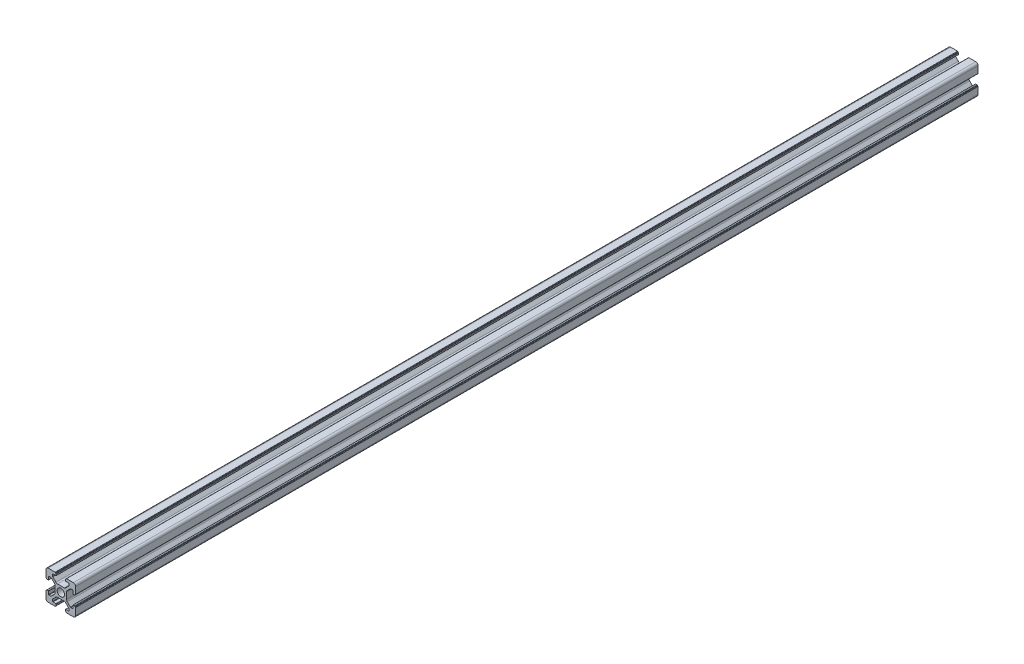
SolidWorks part; units mm, degrees
ref_plane "前视基准面" through (0, 0, 0) normal (0, 0, 1) x (1, 0, 0)
ref_plane "上视基准面" through (0, 0, 0) normal (0, 1, 0) x (1, 0, 0)
ref_plane "右视基准面" through (0, 0, 0) normal (1, 0, 0) x (0, 0, -1)
sketch "草图1" plane through (0, 0, 0) normal (0, 0, 1) x (1, 0, 0)
  line L0 (0, 0) -> (0, 5.5) construction
  line L1 (-8.5023, -10.0023) -> (-3.85, -10.0023)
  line L2 (-10.0023, -8.5023) -> (-10.0023, -3.85)
  line L3 (-8.5023, 10.0023) -> (-3.85, 10.0023)
  line L4 (10.0023, -8.5023) -> (10.0023, -3.85)
  line L5 (-10.0023, -10.0023) -> (10.0023, 10.0023) construction
  line L6 (-10.0023, 10.0023) -> (10.0023, -10.0023) construction
  line L7 (-2.218, -3.9) -> (2.218, -3.9)
  line L8 (-3.9, -2.218) -> (-3.9, 2.218)
  line L9 (-2.218, 3.9) -> (2.218, 3.9)
  line L10 (3.9, -2.218) -> (3.9, 2.218)
  line L11 (-3.9, -3.9) -> (3.9, 3.9) construction
  line L12 (-3.9, 3.9) -> (3.9, -3.9) construction
  line L13 (-5.25, -8.2) -> (-3.35, -8.2)
  line L14 (-8.2, -5.25) -> (-8.2, -3.35)
  line L15 (-5.25, 8.2) -> (-3.35, 8.2)
  line L16 (8.2, -5.25) -> (8.2, -3.35)
  line L17 (-8.2, -8.2) -> (8.2, 8.2) construction
  line L18 (-8.2, 8.2) -> (8.2, -8.2) construction
  line L19 (-7.95, 5.5) -> (-6.6642, 5.5)
  line L20 (0, 0) -> (5.5, 0) construction
  line L23 (-5.5, 7.95) -> (-5.5, 6.6642)
  line L26 (0, 0) -> (-0.5303, 0.5303)
  line L27 (3.2787, 4.3393) -> (5.4268, 6.4874)
  line L28 (0, 0) -> (0.5303, -0.5303)
  line L29 (5.5, 6.6642) -> (5.5, 7.95)
  line L30 (4.3393, 3.2787) -> (6.4874, 5.4268)
  line L31 (6.6642, 5.5) -> (7.95, 5.5)
  line L32 (4.3393, -3.2787) -> (6.4874, -5.4268)
  line L33 (3.2787, -4.3393) -> (5.4268, -6.4874)
  line L34 (-3.2787, -4.3393) -> (-5.4268, -6.4874)
  line L35 (-4.3393, -3.2787) -> (-6.4874, -5.4268)
  line L36 (-4.3393, 3.2787) -> (-6.4874, 5.4268)
  line L37 (-3.2787, 4.3393) -> (-5.4268, 6.4874)
  line L38 (3.1, -8.45) -> (3.1, -9.2523)
  line L39 (8.45, 3.1) -> (9.2523, 3.1)
  line L40 (-5.5, -6.6642) -> (-5.5, -7.95)
  line L41 (-6.6642, -5.5) -> (-7.95, -5.5)
  line L42 (5.5, -6.6642) -> (5.5, -7.95)
  line L43 (6.6642, -5.5) -> (7.95, -5.5)
  line L44 (9.2523, -3.1) -> (8.45, -3.1)
  line L46 (10.0023, 3.85) -> (10.0023, 8.5023)
  line L47 (8.2, 3.35) -> (8.2, 5.25)
  line L48 (-3.1, -9.2523) -> (-3.1, -8.45)
  line L49 (-8.45, -3.1) -> (-9.2523, -3.1)
  line L50 (-9.2523, 3.1) -> (-8.45, 3.1)
  line L51 (-3.1, 8.45) -> (-3.1, 9.2523)
  line L52 (3.1, 9.2523) -> (3.1, 8.45)
  line L53 (3.85, 10.0023) -> (8.5023, 10.0023)
  line L54 (3.35, 8.2) -> (5.25, 8.2)
  line L55 (-10.0023, 3.85) -> (-10.0023, 8.5023)
  line L56 (-8.2, 3.35) -> (-8.2, 5.25)
  line L57 (3.35, -8.2) -> (5.25, -8.2)
  line L58 (3.85, -10.0023) -> (8.5023, -10.0023)
  line L59 (9.7523, -3.6) -> (9.5023, -3.6)
  line L61 (9.7523, 3.6) -> (9.5023, 3.6)
  line L62 (9.5023, -3.6) -> (9.5023, -3.35)
  line L63 (3.6, -9.7523) -> (3.6, -9.5023)
  line L64 (3.35, -9.5023) -> (3.6, -9.5023)
  line L65 (9.5023, 3.35) -> (9.5023, 3.6)
  line L66 (-3.6, -9.5023) -> (-3.35, -9.5023)
  line L67 (-3.6, -9.7523) -> (-3.6, -9.5023)
  line L68 (-9.7523, -3.6) -> (-9.5023, -3.6)
  line L69 (-9.5023, -3.35) -> (-9.5023, -3.6)
  line L70 (-9.5023, 3.6) -> (-9.5023, 3.35)
  line L71 (-9.7523, 3.6) -> (-9.5023, 3.6)
  line L72 (-3.6, 9.7523) -> (-3.6, 9.5023)
  line L73 (-3.35, 9.5023) -> (-3.6, 9.5023)
  line L74 (3.6, 9.5023) -> (3.35, 9.5023)
  line L75 (3.6, 9.7523) -> (3.6, 9.5023)
  circle A0 centre (0, 0) radius 2.5
  arc A1 (10.0023, 8.5023) -> (8.5023, 10.0023) centre (8.5023, 8.5023) ccw
  arc A2 (8.5023, -10.0023) -> (10.0023, -8.5023) centre (8.5023, -8.5023) ccw
  arc A3 (-10.0023, -8.5023) -> (-8.5023, -10.0023) centre (-8.5023, -8.5023) ccw
  arc A4 (-10.0023, 8.5023) -> (-8.5023, 10.0023) centre (-8.5023, 8.5023) cw
  arc A5 (-9.5023, -3.35) -> (-9.2523, -3.1) centre (-9.2523, -3.35) cw
  arc A6 (-9.7523, -3.6) -> (-10.0023, -3.85) centre (-9.7523, -3.85) ccw
  arc A7 (-8.45, -3.1) -> (-8.2, -3.35) centre (-8.45, -3.35) cw
  arc A8 (-7.95, -5.5) -> (-8.2, -5.25) centre (-7.95, -5.25) cw
  arc A9 (-6.4874, -5.4268) -> (-6.6642, -5.5) centre (-6.6642, -5.25) cw
  arc A10 (-5.4268, -6.4874) -> (-5.5, -6.6642) centre (-5.25, -6.6642) ccw
  arc A11 (-5.5, -7.95) -> (-5.25, -8.2) centre (-5.25, -7.95) ccw
  arc A12 (-3.6, -9.7523) -> (-3.85, -10.0023) centre (-3.85, -9.7523) cw
  arc A13 (-3.35, -9.5023) -> (-3.1, -9.2523) centre (-3.35, -9.2523) ccw
  arc A14 (-3.1, -8.45) -> (-3.35, -8.2) centre (-3.35, -8.45) ccw
  arc A15 (3.1, -8.45) -> (3.35, -8.2) centre (3.35, -8.45) cw
  arc A16 (5.5, -7.95) -> (5.25, -8.2) centre (5.25, -7.95) cw
  arc A17 (5.4268, -6.4874) -> (5.5, -6.6642) centre (5.25, -6.6642) cw
  arc A18 (6.4874, -5.4268) -> (6.6642, -5.5) centre (6.6642, -5.25) ccw
  arc A19 (7.95, -5.5) -> (8.2, -5.25) centre (7.95, -5.25) ccw
  arc A20 (8.45, -3.1) -> (8.2, -3.35) centre (8.45, -3.35) ccw
  arc A21 (9.5023, -3.35) -> (9.2523, -3.1) centre (9.2523, -3.35) ccw
  arc A22 (9.7523, -3.6) -> (10.0023, -3.85) centre (9.7523, -3.85) cw
  arc A23 (3.35, -9.5023) -> (3.1, -9.2523) centre (3.35, -9.2523) cw
  arc A24 (3.6, -9.7523) -> (3.85, -10.0023) centre (3.85, -9.7523) ccw
  arc A25 (7.95, 5.5) -> (8.2, 5.25) centre (7.95, 5.25) cw
  arc A26 (8.2, 3.35) -> (8.45, 3.1) centre (8.45, 3.35) ccw
  arc A27 (9.5023, 3.35) -> (9.2523, 3.1) centre (9.2523, 3.35) cw
  arc A28 (9.7523, 3.6) -> (10.0023, 3.85) centre (9.7523, 3.85) ccw
  arc A29 (6.6642, 5.5) -> (6.4874, 5.4268) centre (6.6642, 5.25) ccw
  arc A30 (5.4268, 6.4874) -> (5.5, 6.6642) centre (5.25, 6.6642) ccw
  arc A31 (5.5, 7.95) -> (5.25, 8.2) centre (5.25, 7.95) ccw
  arc A32 (3.1, 8.45) -> (3.35, 8.2) centre (3.35, 8.45) ccw
  arc A33 (3.6, 9.7523) -> (3.85, 10.0023) centre (3.85, 9.7523) cw
  arc A34 (3.35, 9.5023) -> (3.1, 9.2523) centre (3.35, 9.2523) ccw
  arc A35 (-9.7523, 3.6) -> (-10.0023, 3.85) centre (-9.7523, 3.85) cw
  arc A36 (-9.5023, 3.35) -> (-9.2523, 3.1) centre (-9.2523, 3.35) ccw
  arc A37 (-8.45, 3.1) -> (-8.2, 3.35) centre (-8.45, 3.35) ccw
  arc A38 (-8.2, 5.25) -> (-7.95, 5.5) centre (-7.95, 5.25) cw
  arc A39 (-6.4874, 5.4268) -> (-6.6642, 5.5) centre (-6.6642, 5.25) ccw
  arc A40 (-5.4268, 6.4874) -> (-5.5, 6.6642) centre (-5.25, 6.6642) cw
  arc A41 (-5.5, 7.95) -> (-5.25, 8.2) centre (-5.25, 7.95) cw
  arc A42 (-3.1, 8.45) -> (-3.35, 8.2) centre (-3.35, 8.45) cw
  arc A43 (-3.1, 9.2523) -> (-3.35, 9.5023) centre (-3.35, 9.2523) ccw
  arc A44 (-3.6, 9.7523) -> (-3.85, 10.0023) centre (-3.85, 9.7523) ccw
  arc A45 (-4.3393, 3.2787) -> (-3.9, 2.218) centre (-5.4, 2.218) cw
  arc A46 (-3.2787, 4.3393) -> (-2.218, 3.9) centre (-2.218, 5.4) ccw
  arc A47 (3.2787, 4.3393) -> (2.218, 3.9) centre (2.218, 5.4) cw
  arc A48 (4.3393, 3.2787) -> (3.9, 2.218) centre (5.4, 2.218) ccw
  arc A49 (4.3393, -3.2787) -> (3.9, -2.218) centre (5.4, -2.218) cw
  arc A50 (3.2787, -4.3393) -> (2.218, -3.9) centre (2.218, -5.4) ccw
  arc A51 (-4.3393, -3.2787) -> (-3.9, -2.218) centre (-5.4, -2.218) ccw
  arc A52 (-2.218, -3.9) -> (-3.2787, -4.3393) centre (-2.218, -5.4) ccw
  point P0 (0, 0)
  point P7 (10.0023, 0)
  point P62 (0, 0)
  point P76 (0, 0)
  point P92 (-8.2, -5.5)
  point P99 (0, 0)
  point P106 (-5.5, -8.2)
  point P117 (5.5, -8.2)
  point P124 (8.2, -5.5)
  point P137 (8.2, 5.5)
  point P140 (8.2, 3.1)
  point P147 (6.5607, 5.5)
  point P152 (5.5, 8.2)
  point P167 (-8.2, 5.5)
  point P174 (-5.5, 8.2)
  dimension "D1" = 1.5
  dimension "D5" = 0.25
  dimension "D6" = 1.5
  dimension "D2" = 4
  dimension "D3" = 4
  dimension "D4" = 4
extrude "凸台-拉伸1" add sketch "草图1" along normal blind 610 contours A52 L7 A50 L33 A17 L42 A16 L57 A15 L38 A23 L64 L63 A24 L58 A2 L4 A22 L59 L62 A21 L44 A20 L16 A19 L43 A18 L32 A49 L10 A48 L30 A29 L31 A25 L47 A26 L39 A27 L65 L61 A28 L46 A1 L53 A33 L75 L74 A34 L52 A32
